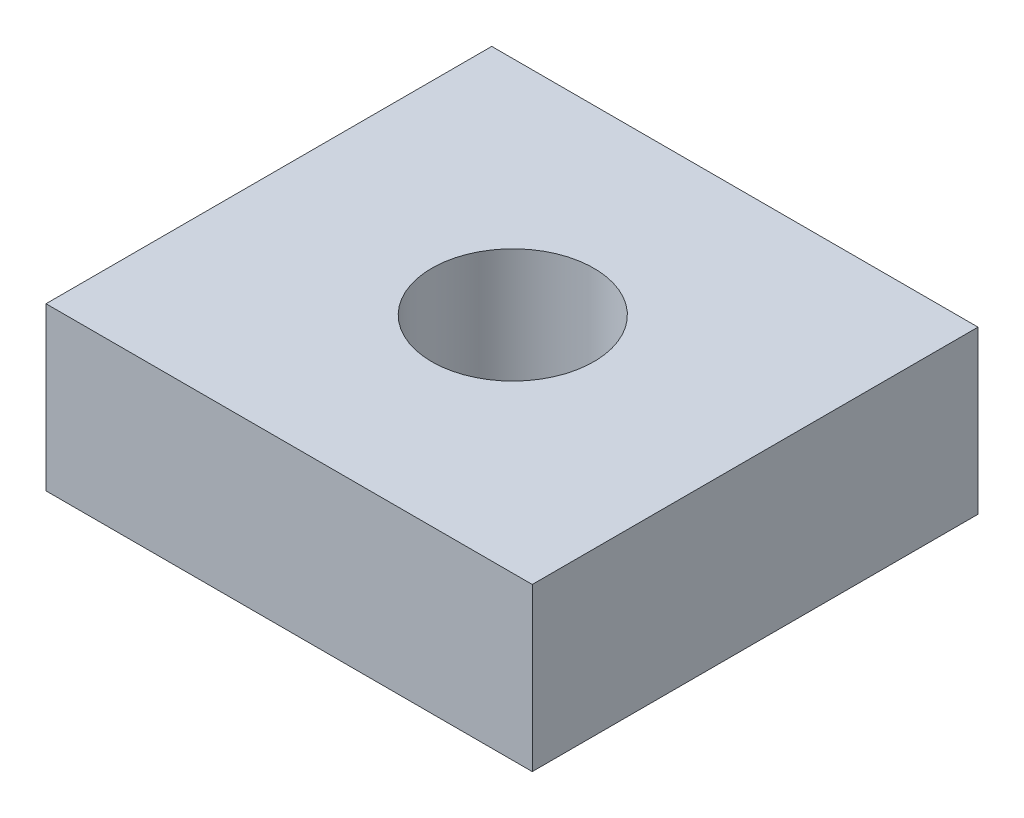
SolidWorks part; units mm, degrees
ref_plane "Front Plane" through (0, 0, 0) normal (0, 0, 1) x (1, 0, 0)
ref_plane "Top Plane" through (0, 0, 0) normal (0, 1, 0) x (1, 0, 0)
ref_plane "Right Plane" through (0, 0, 0) normal (1, 0, 0) x (0, 0, -1)
sketch "Sketch1" plane through (0, 0, 0) normal (0, 1, 0) x (1, 0, 0)
  line L1 (0, 0) -> (76.2, 0)
  line L2 (0, 0) -> (0, 69.85)
  line L3 (0, 69.85) -> (76.2, 69.85)
  line L4 (76.2, 0) -> (76.2, 69.85)
  circle A0 centre (38.1, 35.052) radius 12.7
  dimension "D5" = 25.4
  dimension "D1" = 69.85
  dimension "D2" = 76.2
  dimension "D3" = 35.052
  dimension "D4" = 38.1
extrude "Boss-Extrude1" add sketch "Sketch1" along normal blind 25.4
